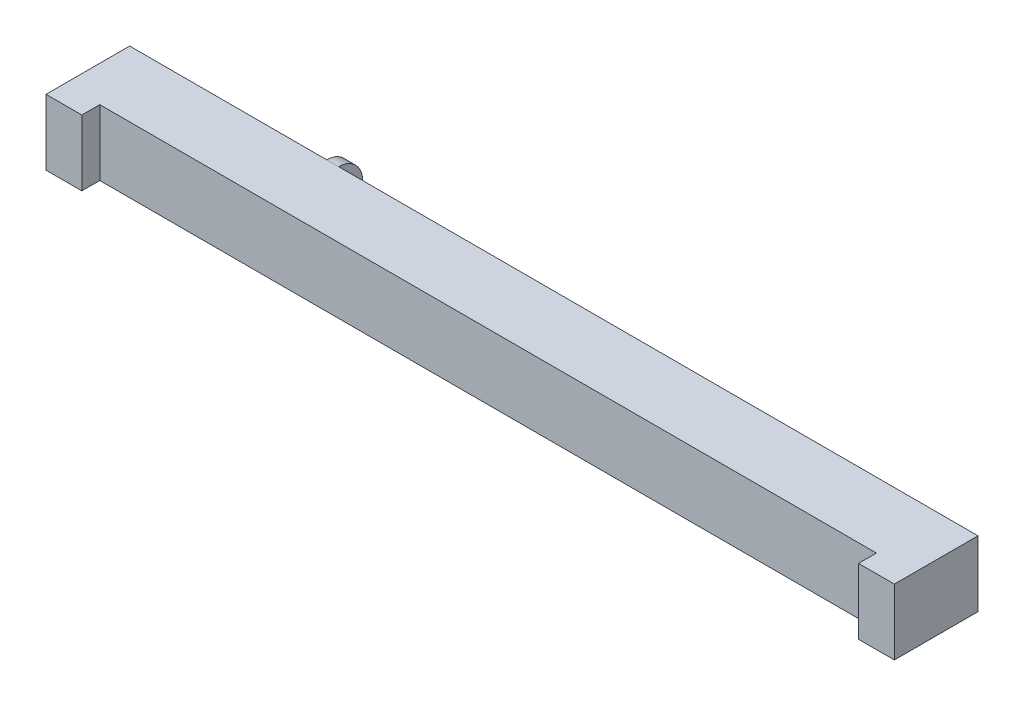
SolidWorks part; units mm, degrees
ref_plane "Alzado" through (0, 0, 0) normal (0, 0, 1) x (1, 0, 0)
ref_plane "Planta" through (0, 0, 0) normal (0, 1, 0) x (1, 0, 0)
ref_plane "Vista lateral" through (0, 0, 0) normal (1, 0, 0) x (0, 0, -1)
sketch "Croquis1" plane through (0, 0, 0) normal (0, 1, 0) x (1, 0, 0)
  line L1 (-35.5, 3.5) -> (35.5, 3.5)
  line L2 (-35.5, 3.5) -> (-35.5, -3.5)
  line L3 (-35.5, -3.5) -> (35.5, -3.5)
  line L4 (35.5, 3.5) -> (35.5, -3.5)
  dimension "D1" = 71
  dimension "D2" = 7
  dimension "D3" = 3.5
  dimension "D4" = 35.5
extrude "Extruir1" add sketch "Croquis1" along normal blind 5.5
sketch "Croquis2" plane through (0, 5.5, 0) normal (0, 1, 0) x (-1, 0, 0)
  line L0 (-35.5, 3.5) -> (-35.5, -3.5) construction
  line L1 (-32.5, 4.7663) -> (32.5, 4.7663)
  line L2 (-32.5, 4.7663) -> (-32.5, 2)
  line L3 (-32.5, 2) -> (32.5, 2)
  line L4 (32.5, 4.7663) -> (32.5, 2)
  line L5 (35.5, -3.5) -> (35.5, 3.5) construction
  line L6 (-35.5, -3.5) -> (35.5, -3.5) construction
  dimension "D1" = 3
  dimension "D2" = 3
  dimension "D3" = 5.5
extrude "Cortar-Extruir1" cut sketch "Croquis2" against normal blind 7.5
sketch "Croquis3" plane through (0, 5.5, 0) normal (0, 1, 0) x (-1, 0, 0)
  line L0 (-35.5, -3.5) -> (35.5, -3.5) construction
  line L1 (-31.5, -3.5) -> (31.5, -3.5)
  line L2 (-31.5, -3.5) -> (-31.5, -5.5)
  line L3 (-31.5, -5.5) -> (31.5, -5.5)
  line L4 (31.5, -3.5) -> (31.5, -5.5)
  line L5 (-32.5, 2) -> (32.5, 2) construction
  line L6 (-35.5, 3.5) -> (-35.5, -3.5) construction
  line L7 (35.5, -3.5) -> (35.5, 3.5) construction
  dimension "D1" = 7.5
  dimension "D2" = 4
  dimension "D3" = 4
extrude "Extruir2" add sketch "Croquis3" against normal up to surface (5.5 mm away) up to face at (0, 0, 1.375)
sketch "Croquis4" plane through (0, 5.5, 0) normal (0, 1, 0) x (-1, 0, 0)
  line L0 (35.5, -3.5) -> (35.5, 3.5) construction
  line L1 (-31.5, -5.5) -> (18, -5.5)
  line L2 (-31.5, -5.5) -> (-31.5, -3.5)
  line L3 (-31.5, -3.5) -> (18, -3.5)
  line L4 (18, -5.5) -> (18, -3.5)
  line L5 (31.5, -5.5) -> (19, -5.5)
  line L6 (31.5, -5.5) -> (31.5, -3.5)
  line L7 (31.5, -3.5) -> (19, -3.5)
  line L8 (19, -5.5) -> (19, -3.5)
  dimension "D1" = 16.5
  dimension "D2" = 1
extrude "Cortar-Extruir2" cut sketch "Croquis4" against normal blind 2.9
fillet "Redondeo1" radius 2 1 edges at (-18.5, 5.5, -5.5)
sketch "Croquis5" plane through (0, 0, -3.5) normal (0, 0, -1) x (-1, 0, 0)
  line L0 (19, 2.6) -> (19, 5.5) construction
  line L1 (34.6707, 4.9341) -> (19, 4.9341)
  line L2 (34.6707, 4.9341) -> (34.6707, 3.1335)
  line L3 (34.6707, 3.1335) -> (19, 3.1335)
  line L4 (19, 4.9341) -> (19, 3.1335)
  line L5 (18, 2.6) -> (18, 5.5) construction
  line L6 (18, 4.9341) -> (-34.7471, 4.9341)
  line L7 (18, 4.9341) -> (18, 3.1335)
  line L8 (18, 3.1335) -> (-34.7471, 3.1335)
  line L9 (-34.7471, 4.9341) -> (-34.7471, 3.1335)
extrude "Cortar-Extruir3" cut sketch "Croquis5" against normal blind 2.9
